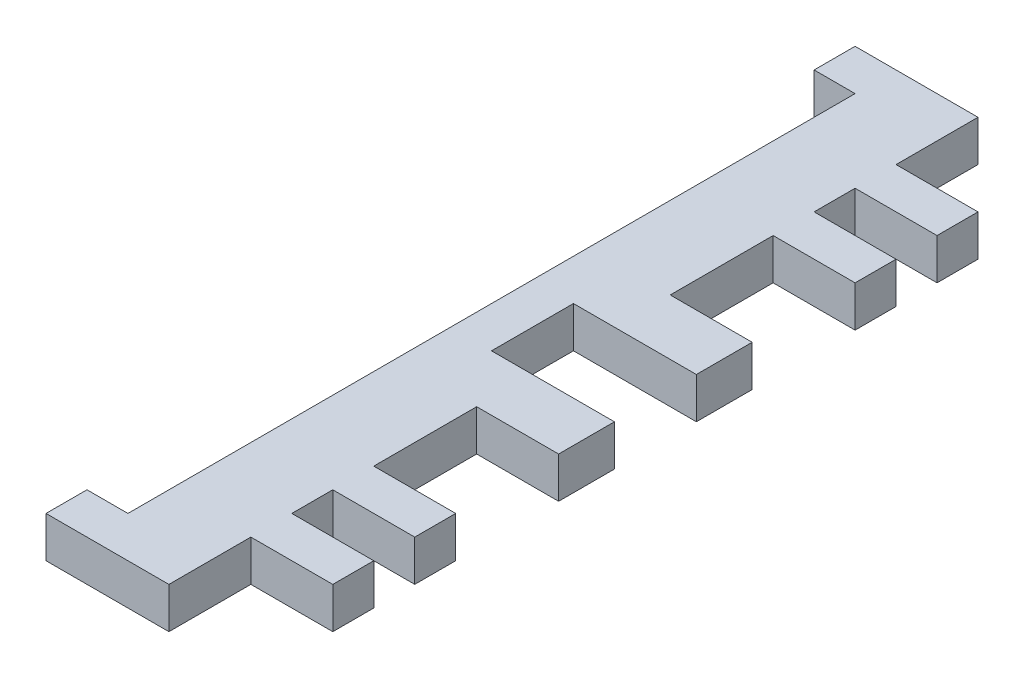
SolidWorks part; units mm, degrees
material "Acrylic (Medium-high impact)"
ref_plane "Front Plane" through (0, 0, 0) normal (0, 0, 1) x (1, 0, 0)
ref_plane "Top Plane" through (0, 0, 0) normal (0, 1, 0) x (1, 0, 0)
ref_plane "Right Plane" through (0, 0, 0) normal (1, 0, 0) x (0, 0, -1)
sketch "Sketch1" plane through (0, 0, 0) normal (0, 1, 0) x (1, 0, 0)
  line L1 (-12.7, -62.7) -> (12.7, -62.7)
  line L2 (-12.7, -62.7) -> (-12.7, 62.7)
  line L3 (-12.7, 62.7) -> (12.7, 62.7)
  line L4 (12.7, -62.7) -> (12.7, 62.7)
  line L5 (-12.7, -62.7) -> (12.7, 62.7) construction
  line L6 (-12.7, 62.7) -> (12.7, -62.7) construction
  point P0 (0, 0)
  dimension "D1" = 125.4
  dimension "D2" = 25.4
extrude "Boss-Extrude1" add sketch "Sketch1" along normal blind 6.35
sketch "Sketch2" plane through (-12.7, 0, 0) normal (-1, 0, 0) x (0, 0, 1)
  line L0 (56.35, 0) -> (56.35, 6.35)
  line L1 (56.35, 0) -> (-56.35, 0)
  line L2 (56.35, 6.35) -> (-56.35, 6.35)
  line L3 (-56.35, 0) -> (-56.35, 6.35)
  line L4 (56.35, 0) -> (-56.35, 6.35) construction
  line L5 (56.35, 6.35) -> (-56.35, 0) construction
  line L6 (62.7, 0) -> (-62.7, 0) construction
  point P1 (0, 3.175)
  dimension "D1" = 6.35
  dimension "D2" = 3.175
  dimension "D3" = 112.7
extrude "Cut-Extrude1" cut sketch "Sketch2" against normal blind 12.7
sketch "Sketch3" plane through (12.7, 0, 0) normal (1, 0, 0) x (0, 0, -1)
  line L0 (-62.7, 6.35) -> (62.7, 6.35) construction
  line L1 (-6.35, 0) -> (6.35, 0)
  line L2 (-6.35, 0) -> (-6.35, 6.35)
  line L3 (-6.35, 6.35) -> (6.35, 6.35)
  line L4 (6.35, 0) -> (6.35, 6.35)
  line L5 (-6.35, 0) -> (6.35, 6.35) construction
  line L6 (-6.35, 6.35) -> (6.35, 0) construction
  line L7 (-62.7, 0) -> (62.7, 0) construction
  line L8 (-62.7, 6.35) -> (-62.7, 0) construction
  point P0 (0, 3.175)
  dimension "D1" = 0
  dimension "D2" = 0
  dimension "D3" = 12.7
  dimension "D4" = 62.7
extrude "Cut-Extrude2" cut sketch "Sketch3" against normal blind 6.35
sketch "Sketch4" plane through (12.7, 0, 0) normal (1, 0, 0) x (0, 0, -1)
  line L0 (-62.7, 6.35) -> (-6.35, 6.35) construction
  line L1 (-6.35, 0) -> (-15, 0)
  line L2 (-6.35, 0) -> (-6.35, 6.35)
  line L3 (-6.35, 6.35) -> (-15, 6.35)
  line L4 (-15, 0) -> (-15, 6.35)
  line L5 (-6.35, 0) -> (-15, 6.35) construction
  line L6 (-6.35, 6.35) -> (-15, 0) construction
  line L7 (-62.7, 0) -> (-6.35, 0) construction
  line L8 (-6.35, 6.35) -> (-6.35, 0) construction
  point P0 (-10.675, 3.175)
  dimension "D1" = 0
  dimension "D2" = 0
  dimension "D3" = 8.65
  dimension "D4" = 0
extrude "Boss-Extrude2" add sketch "Sketch4" along normal blind 12.7
mirror "Mirror1" about plane through (0, 0, 0) normal (0, 0, 1) of "Boss-Extrude2"
sketch "Sketch5" plane through (12.7, 0, 0) normal (1, 0, 0) x (0, 0, -1)
  line L0 (15, 6.35) -> (62.7, 6.35) construction
  line L1 (43.65, 0) -> (50, 0)
  line L2 (43.65, 0) -> (43.65, 6.35)
  line L3 (43.65, 6.35) -> (50, 6.35)
  line L4 (50, 0) -> (50, 6.35)
  line L5 (43.65, 0) -> (50, 6.35) construction
  line L6 (43.65, 6.35) -> (50, 0) construction
  line L7 (15, 0) -> (62.7, 0) construction
  line L8 (62.7, 6.35) -> (62.7, 0) construction
  point P0 (46.825, 3.175)
  dimension "D1" = 0
  dimension "D2" = 0
  dimension "D3" = 12.7
  dimension "D4" = 6.35
extrude "Boss-Extrude3" add sketch "Sketch5" along normal blind 12.7
sketch "Sketch6" plane through (12.7, 0, 0) normal (1, 0, 0) x (0, 0, -1)
  line L0 (43.65, 6.35) -> (43.65, 0) construction
  line L1 (30.95, 0) -> (37.3, 0)
  line L2 (30.95, 0) -> (30.95, 6.35)
  line L3 (30.95, 6.35) -> (37.3, 6.35)
  line L4 (37.3, 0) -> (37.3, 6.35)
  line L5 (30.95, 0) -> (37.3, 6.35) construction
  line L6 (30.95, 6.35) -> (37.3, 0) construction
  line L7 (15, 6.35) -> (43.65, 6.35) construction
  line L8 (15, 0) -> (43.65, 0) construction
  point P0 (34.125, 3.175)
  dimension "D1" = 6.35
  dimension "D2" = 0
  dimension "D3" = 0
  dimension "D4" = 6.35
extrude "Boss-Extrude4" add sketch "Sketch6" along normal blind 12.7
mirror "Mirror2" about plane through (0, 0, 0) normal (0, 0, 1) of "Boss-Extrude4", "Boss-Extrude3"
sketch "Sketch10" plane through (0, 6.35, 0) normal (0, 1, 0) x (1, 0, 0)
  line L0 (0, 56.35) -> (-12.7, 56.35) construction
  line L1 (-12.7, 62.7) -> (-6.35, 62.7)
  line L2 (-12.7, 62.7) -> (-12.7, 56.35)
  line L3 (-12.7, 56.35) -> (-6.35, 56.35)
  line L4 (-6.35, 62.7) -> (-6.35, 56.35)
  dimension "D1" = 6.35
extrude "Cut-Extrude3" cut sketch "Sketch10" against normal through all
mirror "Mirror3" about plane through (0, 0, 0) normal (0, 0, 1) of "Cut-Extrude3"
